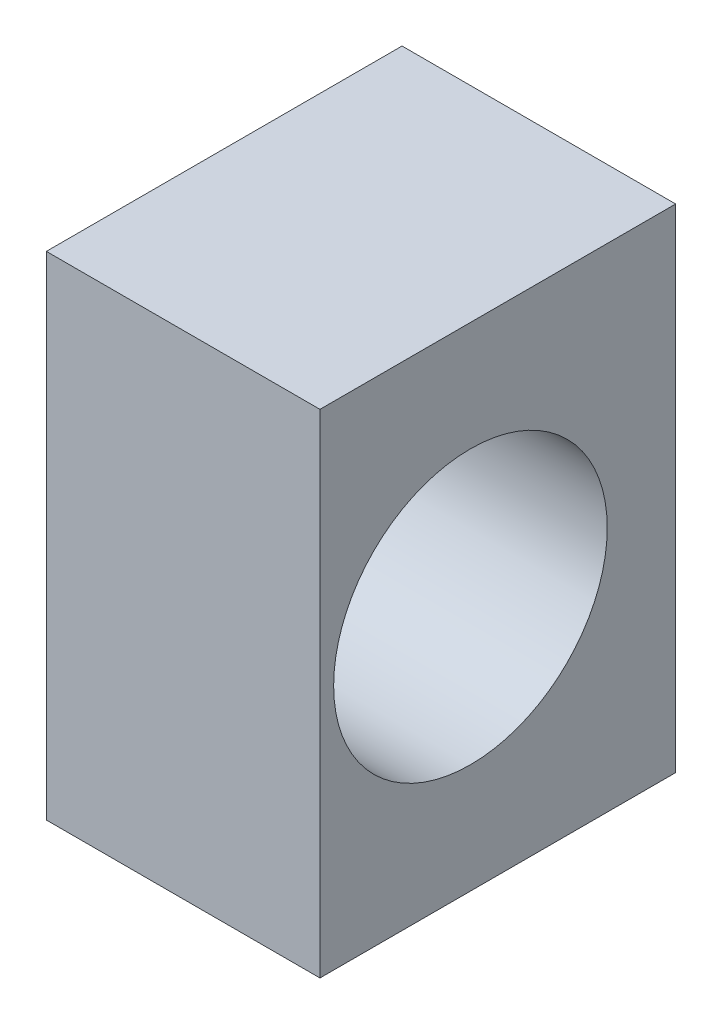
SolidWorks part; units mm, degrees
ref_plane "Face" through (0, 0, 0) normal (0, 0, 1) x (1, 0, 0)
ref_plane "Dessus" through (0, 0, 0) normal (0, 1, 0) x (1, 0, 0)
ref_plane "Droite" through (0, 0, 0) normal (1, 0, 0) x (0, 0, -1)
sketch "Esquisse1" plane through (0, 0, 0) normal (1, 0, 0) x (0, 0, -1)
  line L1 (0, 0) -> (13, 0)
  line L2 (0, 0) -> (0, 18)
  line L3 (0, 18) -> (13, 18)
  line L4 (13, 0) -> (13, 18)
  dimension "D1" = 18
  dimension "D2" = 13
extrude "Extrusion1" add sketch "Esquisse1" along normal blind 10
sketch "Esquisse2" plane through (0, 0, 0) normal (-1, 0, 0) x (0, 0, 1)
  line L0 (-13, 18) -> (0, 18) construction
  line L1 (0, 18) -> (0, 0) construction
  circle A0 centre (-5.5, 9) radius 5
  dimension "D1" = 10
  dimension "D2" = 9
  dimension "D3" = 5.5
extrude "Enlèv. mat.-Extru.1" cut sketch "Esquisse2" against normal through all
